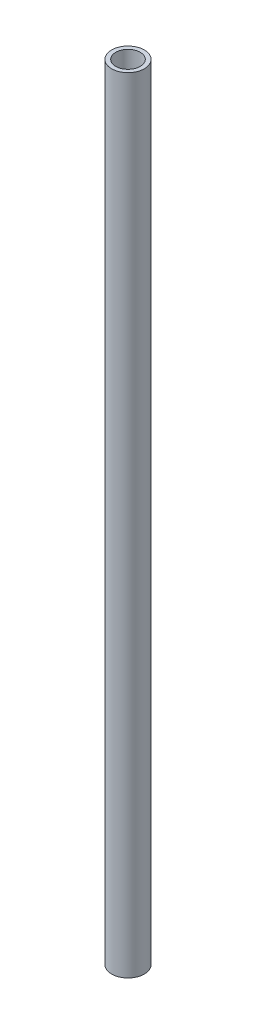
SolidWorks part; units mm, degrees
material "PVC Rigid"
ref_plane "Front Plane" through (0, 0, 0) normal (0, 0, 1) x (1, 0, 0)
ref_plane "Top Plane" through (0, 0, 0) normal (0, 1, 0) x (1, 0, 0)
ref_plane "Right Plane" through (0, 0, 0) normal (1, 0, 0) x (0, 0, -1)
sketch "Sketch1" plane through (0, 0, 0) normal (0, 1, 0) x (1, 0, 0)
  circle A0 centre (0, 0) radius 9.525
  circle A1 centre (0, 0) radius 12.7
  dimension "D1" = 19.05
  dimension "D2" = 25.4
extrude "Boss-Extrude1" add sketch "Sketch1" along normal blind 609.6
